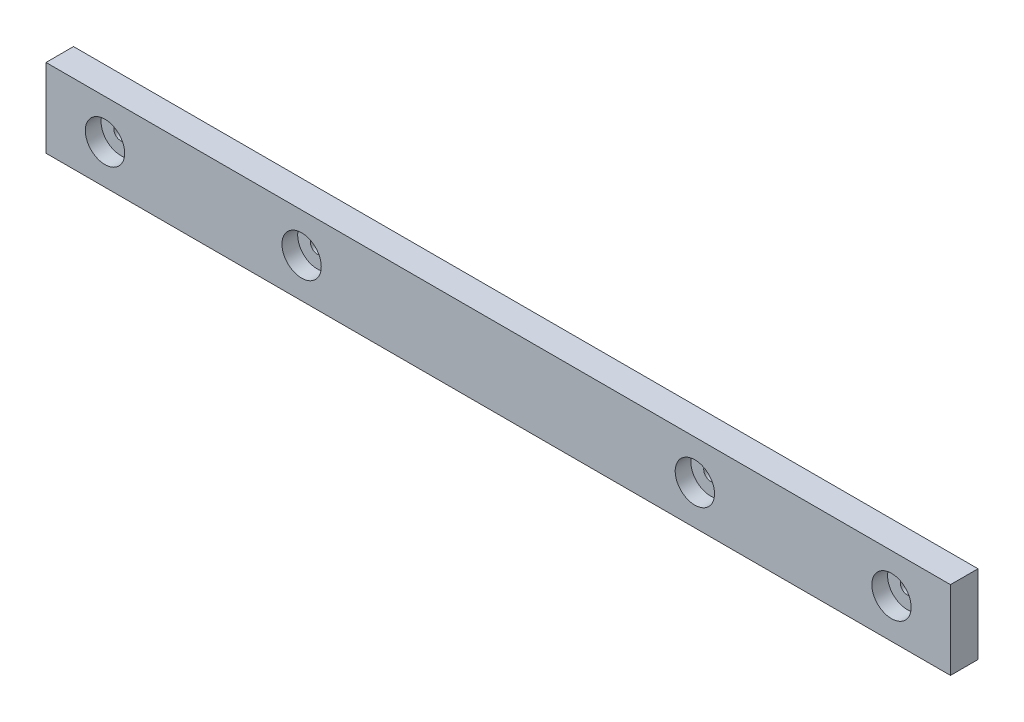
SolidWorks part; units mm, degrees
ref_plane "Front Plane" through (0, 0, 0) normal (0, 0, 1) x (1, 0, 0)
ref_plane "Top Plane" through (0, 0, 0) normal (0, 1, 0) x (1, 0, 0)
ref_plane "Right Plane" through (0, 0, 0) normal (1, 0, 0) x (0, 0, -1)
sketch "Sketch1" plane through (0, 0, 0) normal (0, 0, 1) x (1, 0, 0)
  line L1 (-115, 10) -> (115, 10)
  line L2 (-115, 10) -> (-115, -10)
  line L3 (-115, -10) -> (115, -10)
  line L4 (115, 10) -> (115, -10)
  line L5 (-115, 10) -> (115, -10) construction
  line L6 (-115, -10) -> (115, 10) construction
  point P0 (0, 0)
  dimension "D1" = 230
  dimension "D2" = 20
extrude "Boss-Extrude1" add sketch "Sketch1" along normal blind 7
sketch "Sketch2" plane through (0, 0, 7) normal (0, 0, 1) x (1, 0, 0)
  line L0 (-50, 0) -> (50, 0) construction
  line L1 (50, 0) -> (100, 0) construction
  line L3 (-100, 0) -> (-50, 0) construction
  circle A0 centre (-100, 0) radius 1.75
  circle A1 centre (100, 0) radius 1.75
  circle A2 centre (50, 0) radius 1.75
  circle A3 centre (-50, 0) radius 1.75
  point P8 (0, 0)
  dimension "D4" = 3.5
  dimension "D5" = 3.5
  dimension "D6" = 3.5
  dimension "D7" = 3.5
  dimension "D1" = 100
  dimension "D2" = 50
  dimension "D3" = 50
extrude "Cut-Extrude1" cut sketch "Sketch2" against normal through all
sketch "Sketch3" plane through (0, 0, 7) normal (0, 0, 1) x (1, 0, 0)
  circle A0 centre (-100, 0) radius 5
  circle A1 centre (-50, 0) radius 5
  circle A2 centre (50, 0) radius 5
  circle A3 centre (100, 0) radius 5
extrude "Cut-Extrude2" cut sketch "Sketch3" against normal blind 4
